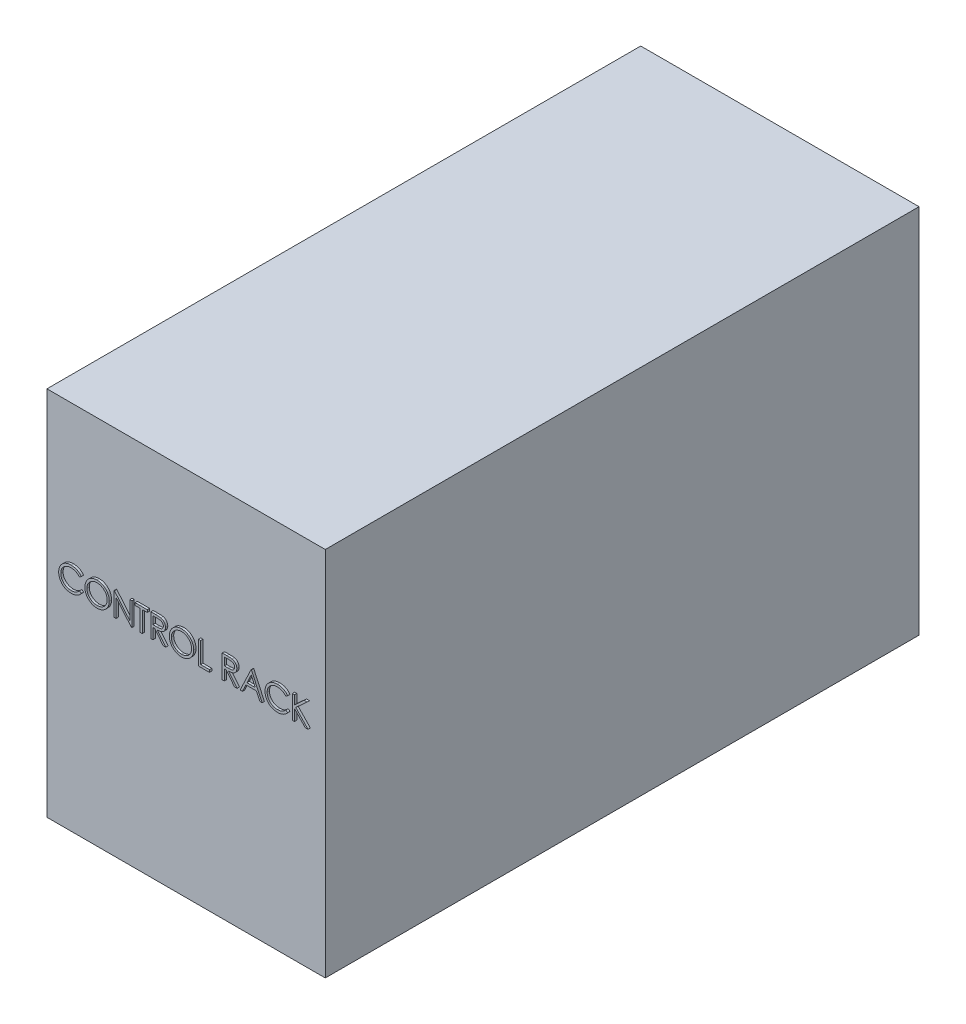
SolidWorks part; units mm, degrees
ref_plane "Front Plane" through (0, 0, 0) normal (0, 0, 1) x (1, 0, 0)
ref_plane "Top Plane" through (0, 0, 0) normal (0, 1, 0) x (1, 0, 0)
ref_plane "Right Plane" through (0, 0, 0) normal (1, 0, 0) x (0, 0, -1)
sketch "Sketch1" plane through (0, 0, 0) normal (0, 0, 1) x (1, 0, 0)
  line L1 (0, 0) -> (-600, 0)
  line L2 (0, 0) -> (0, 800)
  line L3 (0, 800) -> (-600, 800)
  line L4 (-600, 0) -> (-600, 800)
  dimension "D1" = 600
  dimension "D2" = 800
extrude "Boss-Extrude1" add sketch "Sketch1" along normal blind 1280
sketch "Sketch2" plane through (0, 0, 1280) normal (0, 0, 1) x (1, 0, 0)
  text T0 "CONTROL RACK" font "Century Gothic" height 50
extrude "Boss-Extrude2" add sketch "Sketch2" along normal blind 5
